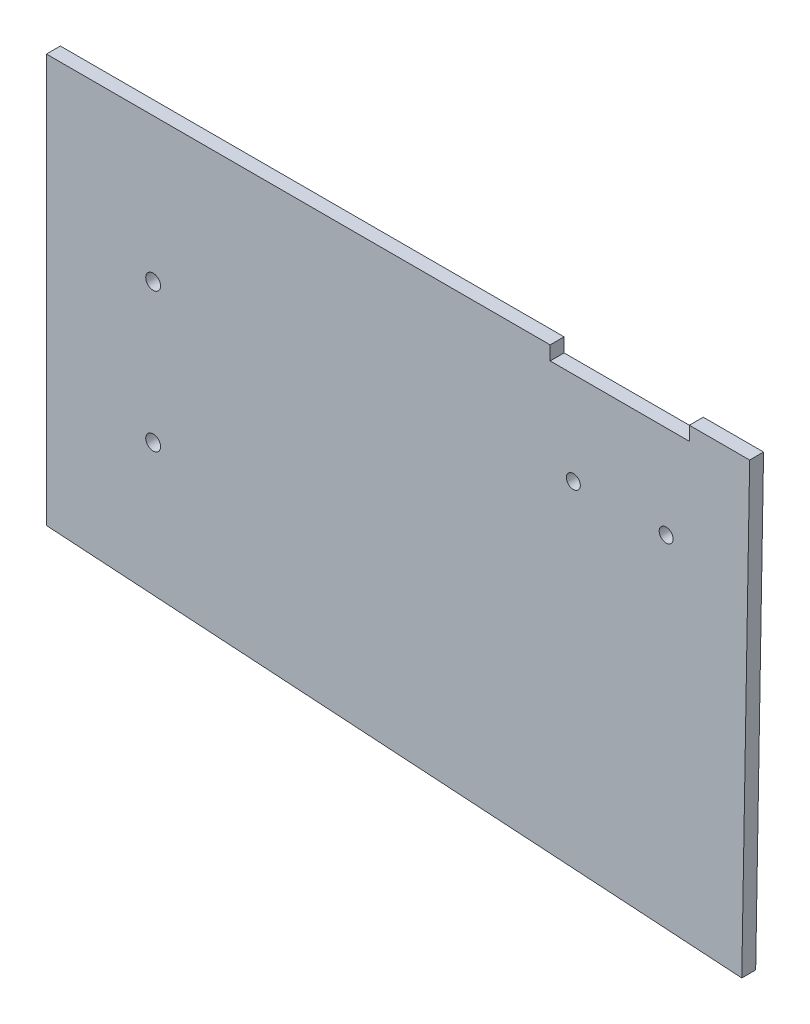
SolidWorks part; units mm, degrees
material "Acrylic (Medium-high impact)"
ref_plane "前视基准面" through (0, 0, 0) normal (0, 0, 1) x (1, 0, 0)
ref_plane "上视基准面" through (0, 0, 0) normal (0, 1, 0) x (1, 0, 0)
ref_plane "右视基准面" through (0, 0, 0) normal (1, 0, 0) x (0, 0, -1)
sketch "Sketch1" plane through (0, 0, 0) normal (0, 0, 1) x (1, 0, 0)
  line L0 (-329.0603, 3) -> (-39.3723, 3) construction
  line L1 (-33.3553, 3) -> (118.2082, 3)
  line L2 (-33.3553, 3) -> (-33.3553, -85)
  line L3 (-33.3553, -85) -> (116.5058, -94.5262)
  line L4 (118.2082, 3) -> (116.5058, -94.5262)
  line L5 (-35.3553, -3) -> (-35.3553, 0) construction
  line L11 (120.2082, 0) -> (120.2082, -3) construction
  point P8 (113.8187, -94.5286)
  point P9 (116.5152, -94.5264)
  point P10 (118.2082, -97.3342)
  point P11 (0, 0)
  point P12 (0, 0)
  point P13 (118.2082, -95.5302)
  point P14 (118.2082, -94.7214)
  point P15 (118.2082, -95)
  point P16 (-33.3553, -85.4239)
  point P17 (118.2082, -95)
  point P18 (0, 0)
  dimension "D1" = 2
  dimension "D2" = 89
  dimension "D3" = 88
  dimension "D4" = 87.363
  dimension "D5" = 2
extrude "Boss-Extrude1" add sketch "Sketch1" along normal blind 3
sketch "Sketch2" plane through (0, 0, 3) normal (0, 0, 1) x (1, 0, 0)
  line L0 (75.2082, 0) -> (105.2082, 0)
  line L1 (105.2082, 0) -> (105.2082, 3)
  line L2 (105.2082, 3) -> (75.2082, 3)
  line L3 (75.2082, 3) -> (75.2082, 0)
  line L4 (-33.3553, 3) -> (-33.3553, -85)
  line L5 (-33.3553, -85) -> (116.5058, -94.5262)
  line L6 (116.5058, -94.5262) -> (118.2082, 3)
  line L7 (118.2082, 3) -> (-33.3553, 3)
  line L8 (-33.3553, 3) -> (-33.3553, -85)
  line L9 (-33.3553, -85) -> (116.5058, -94.5262)
  line L10 (116.5058, -94.5262) -> (118.2082, 3)
  line L11 (118.2082, 3) -> (-33.3553, 3)
  circle A0 centre (80.2082, -20) radius 1.5 construction
  circle A1 centre (100.2082, -20) radius 1.5 construction
  circle A2 centre (80.2082, -20) radius 1.5
  circle A3 centre (100.2082, -20) radius 1.5
  line M8 (118.2082, 3) -> (-33.3553, 3)
  dimension "D1" = 0
extrude "Cut-Extrude1" cut sketch "Sketch2" against normal blind 3 contours L3 L0 L1 M8 | A2 | A3
sketch "Sketch3" plane through (0, 0, 0) normal (0, 0, -1) x (-1, 0, 0)
  circle A0 centre (10.3553, -28) radius 1.6 construction
  circle A1 centre (10.3553, -58) radius 1.6 construction
  circle A2 centre (10.3553, -28) radius 1.6
  circle A3 centre (10.3553, -58) radius 1.6
extrude "Cut-Extrude2" cut sketch "Sketch3" against normal blind 3
